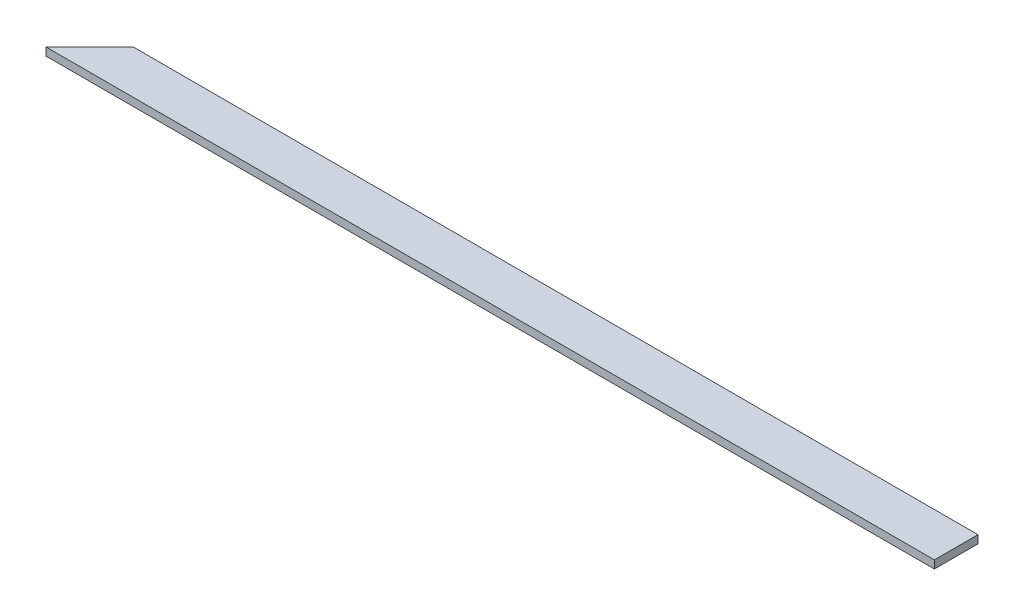
SolidWorks part; units mm, degrees
ref_plane "Front Plane" through (0, 0, 0) normal (0, 0, 1) x (1, 0, 0)
ref_plane "Top Plane" through (0, 0, 0) normal (0, 1, 0) x (1, 0, 0)
ref_plane "Right Plane" through (0, 0, 0) normal (1, 0, 0) x (0, 0, -1)
sketch "Sketch1" plane through (0, 0, 0) normal (0, 1, 0) x (1, 0, 0)
  line L0 (0, 0) -> (139.7, 139.7)
  line L1 (0, 0) -> (2844.8, 0)
  line L3 (139.7, 139.7) -> (2705.1, 139.7)
  line L5 (2844.8, 0) -> (2705.1, 0)
  line L6 (2844.8, 0) -> (2844.8, 139.7)
  line L7 (2844.8, 139.7) -> (2705.1, 139.7)
  dimension "D1" = 2844.8
  dimension "D2" = 139.7
  dimension "D3" = 45
extrude "Boss-Extrude1" add sketch "Sketch1" along normal blind 25.4 contours L6 L7 L3 L0 L1
